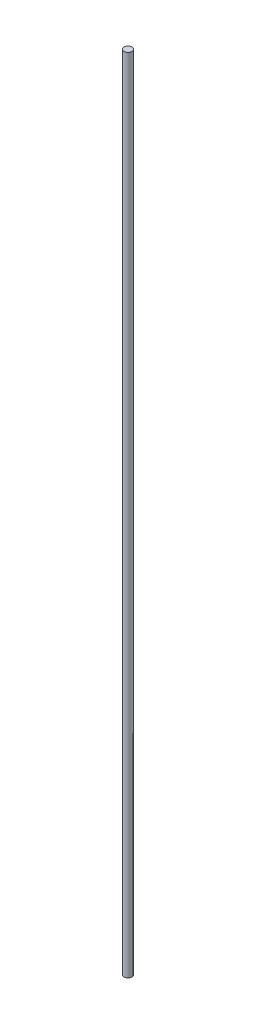
SolidWorks part; units mm, degrees
ref_plane "Front Plane" through (0, 0, 0) normal (0, 0, 1) x (1, 0, 0)
ref_plane "Top Plane" through (0, 0, 0) normal (0, 1, 0) x (1, 0, 0)
ref_plane "Right Plane" through (0, 0, 0) normal (1, 0, 0) x (0, 0, -1)
sketch "Sketch1" plane through (0, 0, 0) normal (0, 1, 0) x (1, 0, 0)
  circle A0 centre (0, 0) radius 0.95
extrude "Boss-Extrude1" add sketch "Sketch1" along normal blind 194
